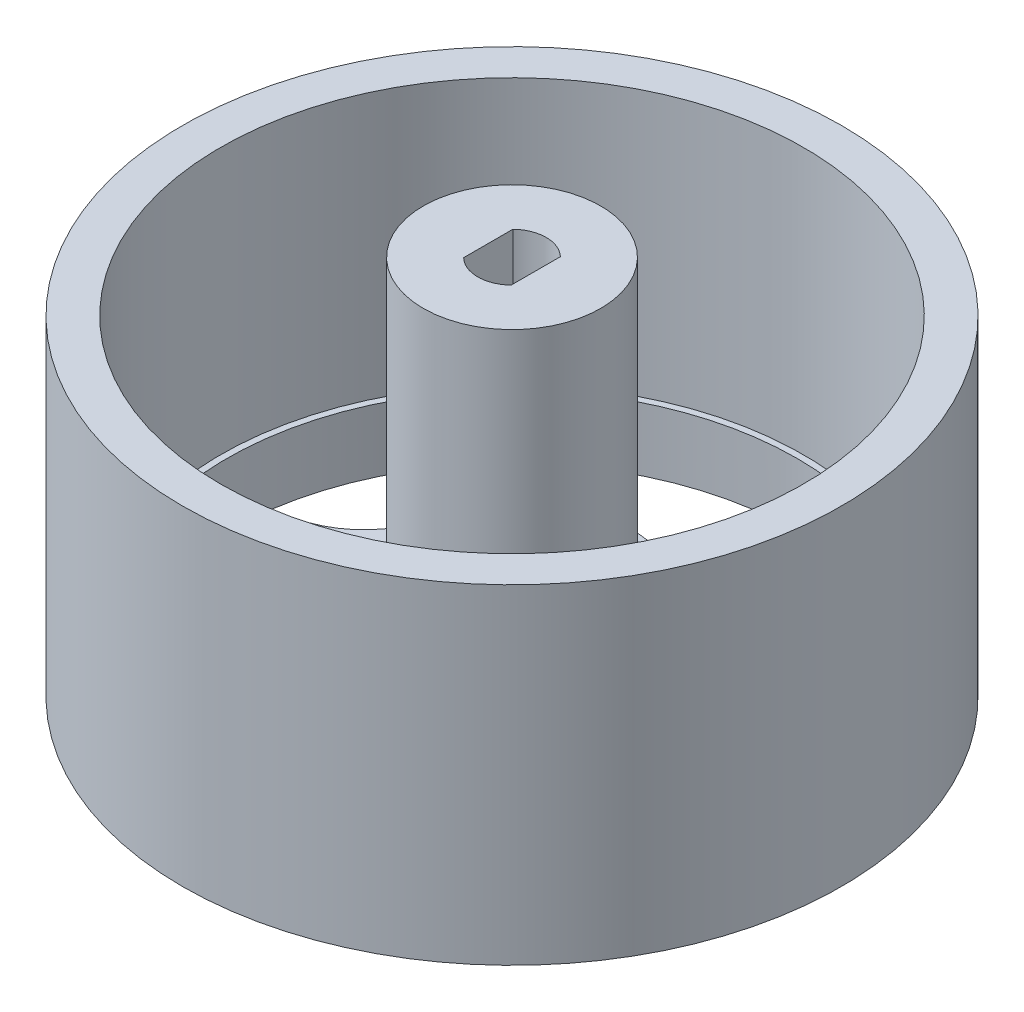
SolidWorks part; units mm, degrees
ref_plane "Front Plane" through (0, 0, 0) normal (0, 0, 1) x (1, 0, 0)
ref_plane "Top Plane" through (0, 0, 0) normal (0, 1, 0) x (1, 0, 0)
ref_plane "Right Plane" through (0, 0, 0) normal (1, 0, 0) x (0, 0, -1)
sketch "Sketch1" plane through (0, 0, 0) normal (0, 1, 0) x (1, 0, 0)
  circle A0 centre (0, 0) radius 26
extrude "Boss-Extrude1" add sketch "Sketch1" along normal blind 26
sketch "Sketch2" plane through (0, 26, 0) normal (0, 1, 0) x (1, 0, 0)
  circle A0 centre (0, 0) radius 23
extrude "Cut-Extrude1" cut sketch "Sketch2" against normal blind 21
sketch "Sketch3" plane through (0, 0, 0) normal (0, -1, 0) x (1, 0, 0)
  line L0 (-3.2574, 22.263) -> (-3.5, 14.5014)
  line L1 (-20.1667, 9.9776) -> (-12.7101, 7.8099)
  line L2 (20.1667, 9.9776) -> (12.7101, 7.8099)
  line L3 (3.2574, 22.263) -> (3.5, 14.5014)
  line L4 (15.7211, -16.0965) -> (11.3553, -9.6746)
  line L5 (22.1799, 3.7817) -> (14.8732, 1.1525)
  line L6 (-10.4505, -19.9258) -> (-5.6921, -13.7891)
  line L7 (-22.1799, 3.7817) -> (-14.8732, 1.1525)
  line L8 (10.4505, -19.9258) -> (5.6921, -13.7891)
  line L9 (-15.7211, -16.0965) -> (-11.3553, -9.6746)
  arc A0 (-22.1799, 3.7817) -> (-15.7211, -16.0965) centre (0, 0) ccw
  arc A1 (-3.2574, 22.263) -> (-20.1667, 9.9776) centre (0, 0) ccw
  arc A2 (-12.7101, 7.8099) -> (-3.5, 14.5014) centre (-10.6994, 14.7264) ccw
  arc A3 (-11.3553, -9.6746) -> (-14.8732, 1.1525) centre (-17.312, -5.625) ccw
  arc A4 (20.1667, 9.9776) -> (3.2574, 22.263) centre (0, 0) ccw
  arc A5 (3.5, 14.5014) -> (12.7101, 7.8099) centre (10.6994, 14.7264) ccw
  arc A6 (15.7211, -16.0965) -> (22.1799, 3.7817) centre (0, 0) ccw
  arc A7 (14.8732, 1.1525) -> (11.3553, -9.6746) centre (17.312, -5.625) ccw
  arc A8 (-10.4505, -19.9258) -> (10.4505, -19.9258) centre (0, 0) ccw
  arc A9 (5.6921, -13.7891) -> (-5.6921, -13.7891) centre (0, -18.2029) ccw
  dimension "D1" = 5
extrude "Cut-Extrude2" cut sketch "Sketch3" against normal blind 21
sketch "Sketch5" plane through (0, 0, 0) normal (0, 0, 1) x (1, 0, 0)
  line L0 (18.5, 0) -> (22.5, 0)
  line L1 (-26, 0) -> (26, 0) construction
  line L2 (22.5, 0) -> (22.5, 4)
  line L3 (0, 0) -> (0, 2.5)
  line L4 (0, 2.5) -> (5, 2.5)
  line L5 (5, 2.5) -> (5, 4)
  line L6 (5, 4) -> (7.5, 4)
  line L7 (0, 0) -> (9, 0)
  line L8 (9, 0) -> (7.5, 4)
  arc A0 (18.5, 0) -> (22.5, 4) centre (18.5, 4) ccw
  dimension "D1" = 4
revolve "Cut-Revolve1" cut sketch "Sketch5" angle 360 about axis through (0, 26, 0) along (0, -1, 0)
sketch "Sketch6" plane through (0, 5, 0) normal (0, 1, 0) x (1, 0, 0)
  circle A0 centre (0, 0) radius 7
extrude "Boss-Extrude2" add sketch "Sketch6" along normal blind 25
sketch "Sketch7" plane through (0, 30, 0) normal (0, 1, 0) x (1, 0, 0)
  line L2 (-1.875, 0) -> (-1.875, 1.9428)
  line L4 (1.875, 1.9428) -> (1.875, 0)
  line L5 (1.875, 0) -> (1.875, -1.9428)
  line L7 (-1.875, -1.9428) -> (-1.875, 0)
  arc A0 (1.875, 1.9428) -> (-1.875, 1.9428) centre (0, 0) ccw
  arc A1 (-1.875, -1.9428) -> (1.875, -1.9428) centre (0, 0) ccw
extrude "Cut-Extrude3" cut sketch "Sketch7" against normal blind 8
